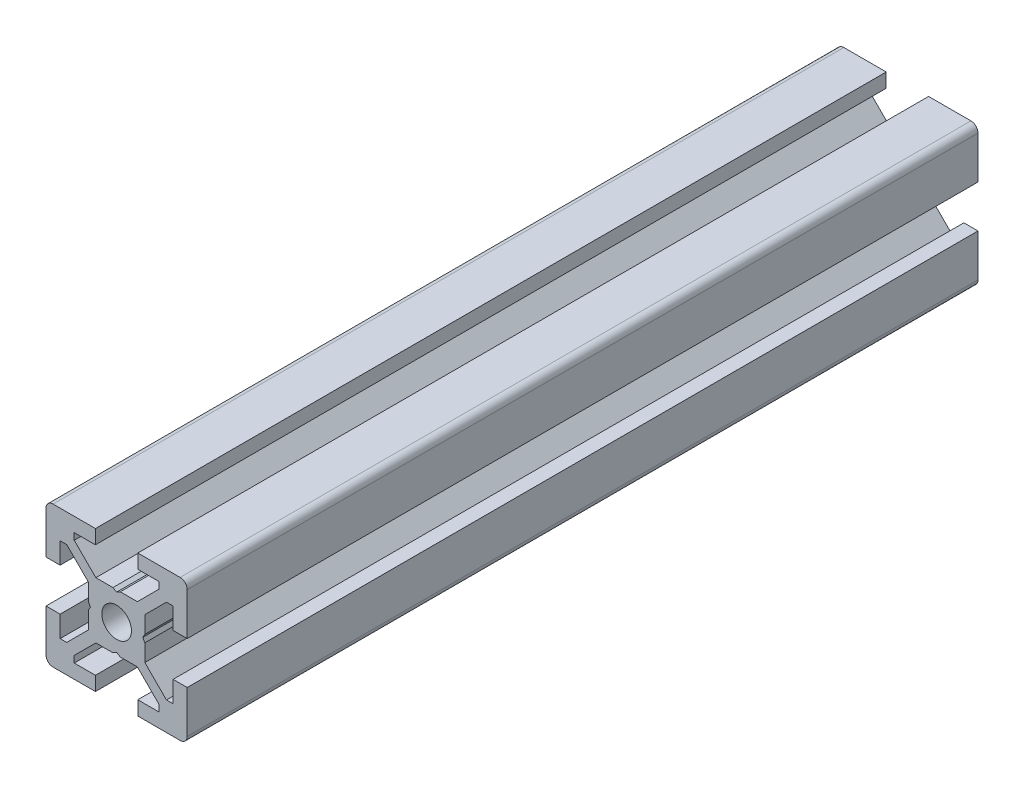
SolidWorks part; units mm, degrees
material "2014 合金"
ref_plane "正面" through (0, 0, 0) normal (0, 0, 1) x (1, 0, 0)
ref_plane "平面" through (0, 0, 0) normal (0, 1, 0) x (1, 0, 0)
ref_plane "右側面" through (0, 0, 0) normal (1, 0, 0) x (0, 0, -1)
ref_plane "平面1" through (0, 0, 0) normal (0, 0, 1) x (1, 0, 0)
sketch "ｽｹｯﾁ1" plane through (0, 0, 0) normal (0, 0, 1) x (1, 0, 0)
  line L0 (-10, -3) -> (-10, -9)
  line L1 (-9, -10) -> (-3, -10)
  line L2 (-3, -10) -> (-3, -8)
  line L3 (-3, -8) -> (-6, -8)
  line L4 (-6, -8) -> (-6, -7.0607)
  line L5 (-6, -7.0607) -> (-2.9393, -4)
  line L6 (-2.9393, -4) -> (-0.5196, -4)
  line L7 (-0.5196, -4) -> (0, -3.7)
  line L8 (0, -3.7) -> (0.5196, -4)
  line L9 (0.5196, -4) -> (2.9393, -4)
  line L10 (2.9393, -4) -> (6, -7.0607)
  line L11 (6, -7.0607) -> (6, -8)
  line L12 (6, -8) -> (3, -8)
  line L13 (3, -8) -> (3, -10)
  line L14 (3, -10) -> (9, -10)
  line L15 (10, -9) -> (10, -3)
  line L16 (10, -3) -> (8, -3)
  line L17 (8, -3) -> (8, -6)
  line L18 (8, -6) -> (7.0607, -6)
  line L19 (7.0607, -6) -> (4, -2.9393)
  line L20 (4, -2.9393) -> (4, -0.5196)
  line L21 (4, -0.5196) -> (3.7, 0)
  line L22 (3.7, 0) -> (4, 0.5196)
  line L23 (4, 0.5196) -> (4, 2.9393)
  line L24 (4, 2.9393) -> (7.0607, 6)
  line L25 (7.0607, 6) -> (8, 6)
  line L26 (8, 6) -> (8, 3)
  line L27 (8, 3) -> (10, 3)
  line L28 (10, 3) -> (10, 9)
  line L29 (9, 10) -> (3, 10)
  line L30 (3, 10) -> (3, 8)
  line L31 (3, 8) -> (6, 8)
  line L32 (6, 8) -> (6, 7.0607)
  line L33 (6, 7.0607) -> (2.9393, 4)
  line L34 (2.9393, 4) -> (0.5196, 4)
  line L35 (0.5196, 4) -> (0, 3.7)
  line L36 (0, 3.7) -> (-0.5196, 4)
  line L37 (-0.5196, 4) -> (-2.9393, 4)
  line L38 (-2.9393, 4) -> (-6, 7.0607)
  line L39 (-6, 7.0607) -> (-6, 8)
  line L40 (-6, 8) -> (-3, 8)
  line L41 (-3, 8) -> (-3, 10)
  line L42 (-3, 10) -> (-9, 10)
  line L43 (-10, 9) -> (-10, 3)
  line L44 (-10, 3) -> (-8, 3)
  line L45 (-8, 3) -> (-8, 6)
  line L46 (-8, 6) -> (-7.0607, 6)
  line L47 (-7.0607, 6) -> (-4, 2.9393)
  line L48 (-4, 2.9393) -> (-4, 0.5196)
  line L49 (-4, 0.5196) -> (-3.7, 0)
  line L50 (-3.7, 0) -> (-4, -0.5196)
  line L51 (-4, -0.5196) -> (-4, -2.9393)
  line L52 (-4, -2.9393) -> (-7.0607, -6)
  line L53 (-7.0607, -6) -> (-8, -6)
  line L54 (-8, -6) -> (-8, -3)
  line L55 (-8, -3) -> (-10, -3)
  arc A0 (-10, -9) -> (-9, -10) centre (-9, -9) ccw
  arc A1 (9, -10) -> (10, -9) centre (9, -9) ccw
  arc A2 (10, 9) -> (9, 10) centre (9, 9) ccw
  arc A3 (-9, 10) -> (-10, 9) centre (-9, 9) ccw
extrude "ﾎﾞｽ - 押し出し1" add sketch "ｽｹｯﾁ1" against normal blind 112
ref_plane "平面2" through (0, 0, 0) normal (1, 0, 0) x (0, 0, -1)
sketch "ｽｹｯﾁ2" plane through (0, 0, 0) normal (1, 0, 0) x (0, 0, -1)
  line L0 (0, 0) -> (0, 2.1)
  line L1 (0, 2.1) -> (260, 2.1)
  line L2 (260, 2.1) -> (260, 0)
  line L3 (260, 0) -> (0, 0)
  line L4 (260, 0) -> (0, 0) construction
revolve "ｶｯﾄ - 回転1" cut sketch "ｽｹｯﾁ2" angle 360 about L4
